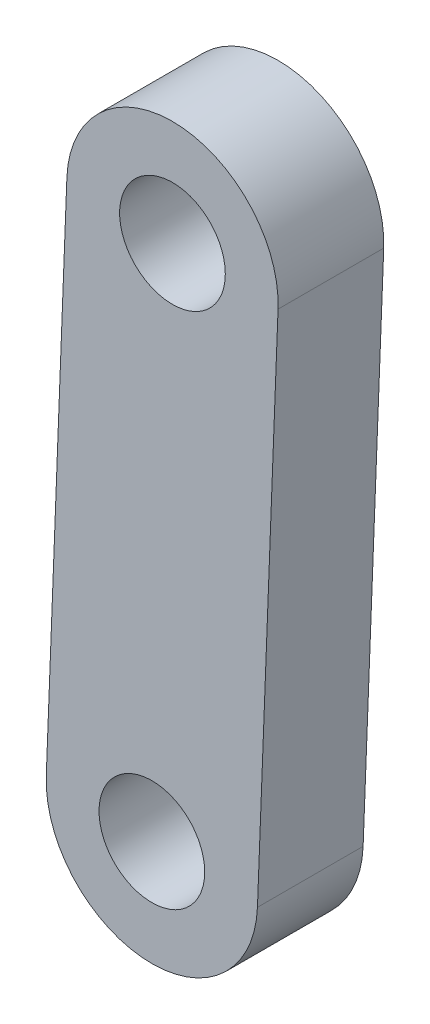
SolidWorks part; units mm, degrees
ref_plane "Front Plane" through (0, 0, 0) normal (0, 0, 1) x (1, 0, 0)
ref_plane "Top Plane" through (0, 0, 0) normal (0, 1, 0) x (1, 0, 0)
ref_plane "Right Plane" through (0, 0, 0) normal (1, 0, 0) x (0, 0, -1)
sketch "Sketch1" plane through (0, 0, 0) normal (0, 0, 1) x (1, 0, 0)
  line L0 (0, 0) -> (-1.9492, -50) construction
  line L1 (9.9924, -0.3895) -> (8.0432, -50.3895)
  line L2 (-9.9924, 0.3895) -> (-11.9416, -49.6105)
  arc A0 (9.9924, -0.3895) -> (-9.9924, 0.3895) centre (0, 0) ccw
  arc A1 (-11.9416, -49.6105) -> (8.0432, -50.3895) centre (-1.9492, -50) ccw
  circle A2 centre (-1.9492, -50) radius 5
  circle A3 centre (0, 0) radius 5
  point P3 (-0.9746, -25)
  dimension "D3" = 10
  dimension "D4" = 10
  dimension "D1" = 50
  dimension "D2" = 20
extrude "Boss-Extrude1" add sketch "Sketch1" along normal blind 10
